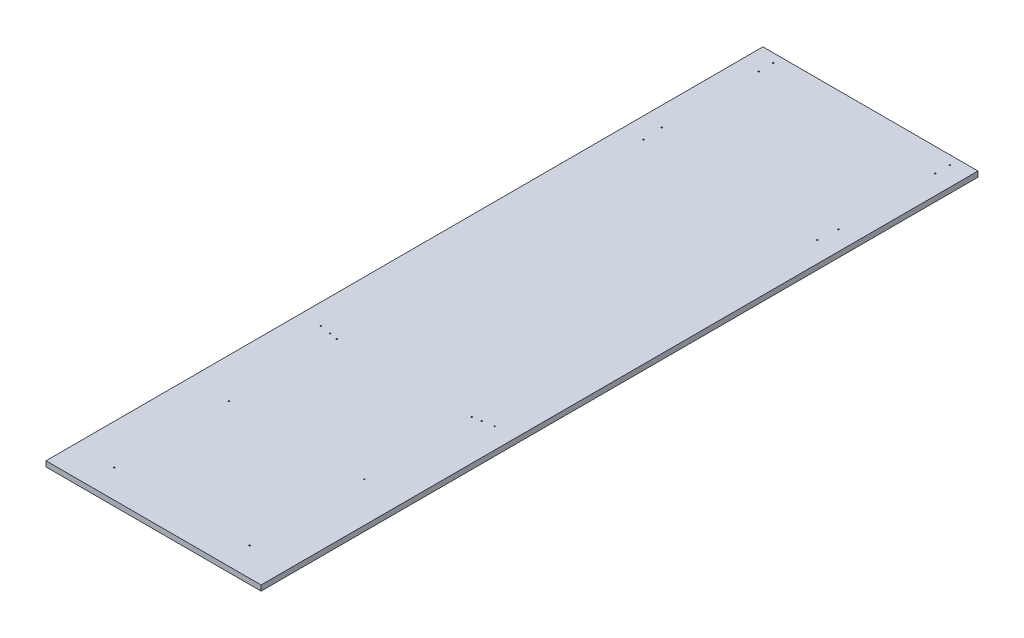
SolidWorks part; units mm, degrees
ref_plane "Front Plane" through (0, 0, 0) normal (0, 0, 1) x (1, 0, 0)
ref_plane "Top Plane" through (0, 0, 0) normal (0, 1, 0) x (1, 0, 0)
ref_plane "Right Plane" through (0, 0, 0) normal (1, 0, 0) x (0, 0, -1)
sketch "Sketch1" plane through (0, 0, 0) normal (0, 1, 0) x (1, 0, 0)
  line L0 (-188.5, -983.5763) -> (-188.5, -252.6333) construction
  line L1 (-300, 1000) -> (300, 1000)
  line L2 (-300, 1000) -> (-300, -1000)
  line L3 (-300, -1000) -> (300, -1000)
  line L4 (300, 1000) -> (300, -1000)
  line L5 (-300, 1000) -> (300, -1000) construction
  line L6 (-300, -1000) -> (300, 1000) construction
  line L7 (-200, -950.7107) -> (-200, -270.7107) construction
  line L8 (188.5, -983.5763) -> (188.5, -252.4974) construction
  line L9 (200, -950.7107) -> (200, -270.7107) construction
  line L10 (-177, -270.7107) -> (-200, -270.7107) construction
  line L11 (200, -270.7107) -> (177, -270.7107) construction
  line L12 (200, -950.7107) -> (177, -950.7107) construction
  line L13 (-177, -950.7107) -> (-200, -950.7107) construction
  line L14 (-211.5, -332.9436) -> (-211.5, -254.4026) construction
  line L15 (-223, -320.7107) -> (-223, -270.7107) construction
  line L16 (-200, -320.7107) -> (-223, -320.7107) construction
  line L17 (211.5, -327.0591) -> (211.5, -252.4974) construction
  line L18 (223, -320.7107) -> (223, -270.7107) construction
  line L19 (223, -320.7107) -> (200, -320.7107) construction
  line L21 (-235, -320.7107) -> (-250, -320.7107) construction
  line L22 (-250, -320.7107) -> (-250, 639.2893) construction
  line L23 (-235, 639.2893) -> (-250, 639.2893) construction
  line L24 (250, -320.7107) -> (235, -320.7107) construction
  line L25 (250, -320.7107) -> (250, 639.2893) construction
  line L26 (250, 639.2893) -> (235, 639.2893) construction
  line L27 (246.5, 635.0226) -> (246.5, 698.3125) construction
  line L28 (235, 689.2893) -> (235, 639.2893) construction
  line L29 (235, 689.2893) -> (258, 689.2893) construction
  line L30 (-246.5, 630.5824) -> (-246.5, 706.8041) construction
  line L31 (-235, 689.2893) -> (-258, 689.2893) construction
  line L32 (-258, 639.2893) -> (-258, 689.2893) construction
  line L33 (-246.5, 911.1491) -> (-246.5, 1020.7138) construction
  line L34 (-235, 919.2893) -> (-258, 919.2893) construction
  line L35 (-235, 990) -> (-258, 990) construction
  line L36 (246.5, 915.8096) -> (246.5, 992.5112) construction
  line L37 (258, 919.2893) -> (235, 919.2893) construction
  line L38 (258, 990) -> (235, 990) construction
  circle A0 centre (-188.5, -920.7107) radius 1.75
  circle A1 centre (188.5, -920.7107) radius 1.75
  circle A2 centre (188.5, -600.7107) radius 1.75
  circle A3 centre (-188.5, -300.7107) radius 1.75
  circle A4 centre (-188.5, -600.7107) radius 1.75
  circle A5 centre (188.5, -300.7107) radius 1.75
  circle A6 centre (-211.5, -295.7107) radius 1.75
  circle A7 centre (211.5, -295.7107) radius 1.75
  circle A8 centre (-242.5, -290.7107) radius 1.75
  circle A9 centre (-242.5, 609.2893) radius 1.75
  circle A10 centre (242.5, -290.7107) radius 1.75
  circle A11 centre (242.5, 609.2893) radius 1.75
  circle A12 centre (246.5, 664.2893) radius 1.75
  circle A13 centre (-246.5, 664.2893) radius 1.75
  circle A14 centre (-246.5, 934.2893) radius 1.75
  circle A15 centre (-246.5, 975) radius 1.75
  circle A16 centre (246.5, 934.2893) radius 1.75
  circle A17 centre (246.5, 975) radius 1.75
  point P0 (0, 0)
  dimension "D6" = 3.5
  dimension "D30" = 3.5
  dimension "D1" = 600
  dimension "D2" = 2000
  dimension "D3" = 11.5
  dimension "D4" = 11.5
  dimension "D5" = 30
  dimension "D7" = 30
  dimension "D8" = 30
  dimension "D9" = 30
  dimension "D10" = 320
  dimension "D11" = 320
  dimension "D12" = 11.5
  dimension "D13" = 25
  dimension "D14" = 11.5
  dimension "D15" = 25
  dimension "D16" = 30
  dimension "D17" = 7.5
  dimension "D18" = 30
  dimension "D19" = 7.5
  dimension "D20" = 30
  dimension "D21" = 7.5
  dimension "D22" = 30
  dimension "D23" = 7.5
  dimension "D24" = 11.5
  dimension "D25" = 25
  dimension "D26" = 25
  dimension "D27" = 11.5
  dimension "D28" = 15
  dimension "D29" = 15
  dimension "D31" = 15
  dimension "D32" = 15
  dimension "D33" = 5
  dimension "D34" = 5
  dimension "D35" = 4
  dimension "D36" = 55
extrude "Boss-Extrude1" add sketch "Sketch1" along normal blind 15
